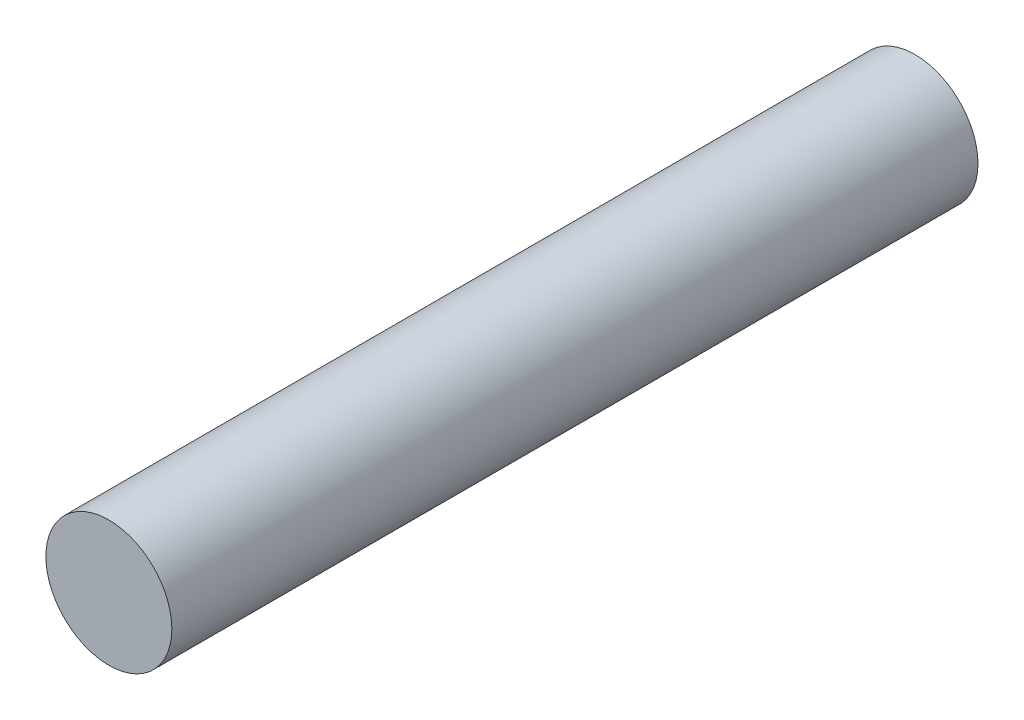
SolidWorks part; units mm, degrees
material "AISI 4130 Steel, normalized at 870C"
ref_plane "Front Plane" through (0, 0, 0) normal (0, 0, 1) x (1, 0, 0)
ref_plane "Top Plane" through (0, 0, 0) normal (0, 1, 0) x (1, 0, 0)
ref_plane "Right Plane" through (0, 0, 0) normal (1, 0, 0) x (0, 0, -1)
sketch "Sketch1" plane through (0, 0, 0) normal (0, 0, 1) x (1, 0, 0)
  circle A0 centre (0, 0) radius 3.9688
  dimension "D1" = 7.9375
extrude "Boss-Extrude1" add sketch "Sketch1" along normal mid plane 50.8
